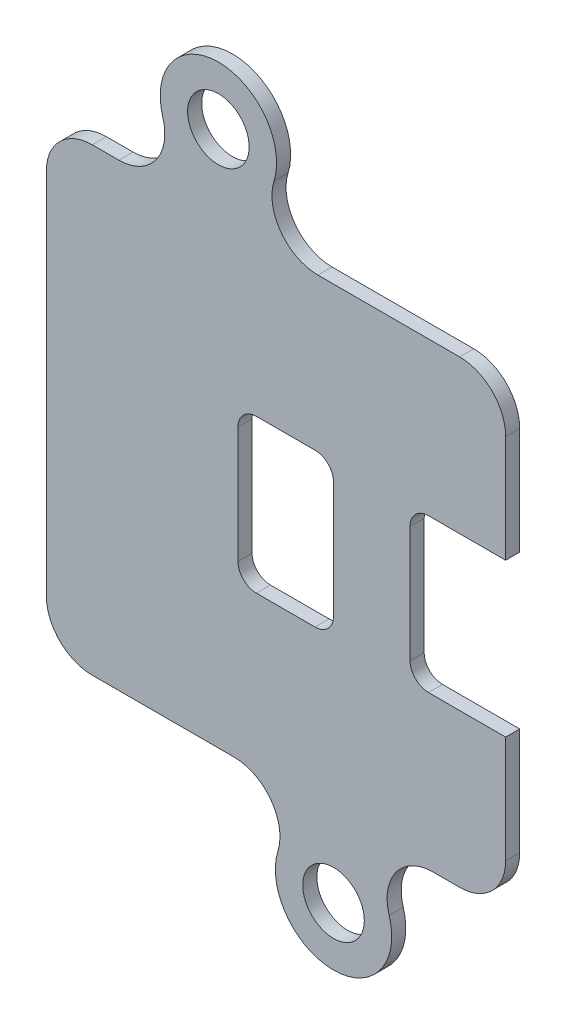
SolidWorks part; units mm, degrees
ref_plane "Front Plane" through (0, 0, 0) normal (0, 0, 1) x (1, 0, 0)
ref_plane "Top Plane" through (0, 0, 0) normal (0, 1, 0) x (1, 0, 0)
ref_plane "Right Plane" through (0, 0, 0) normal (1, 0, 0) x (0, 0, -1)
sketch "Sketch1" plane through (0, 0, 0) normal (0, 0, 1) x (1, 0, 0)
  line L0 (14.2748, 19.05) -> (14.2748, 6.35)
  line L1 (-23.8252, 44.45) -> (-17.8044, 44.45)
  line L2 (-23.8252, 44.45) -> (-23.8252, 6.35)
  line L3 (-23.8252, 6.35) -> (-8.254, 6.35)
  line L4 (14.2748, 44.45) -> (14.2748, 31.75)
  line L5 (14.2748, 31.75) -> (6.35, 31.75)
  line L7 (14.2748, 19.05) -> (6.35, 19.05)
  line L8 (6.35, 31.75) -> (6.35, 19.05)
  line L9 (0, 0) -> (0, 2.5527) construction
  line L10 (0, 0) -> (-50.497, 0) construction
  line L11 (-9.5504, 50.8) -> (-9.5504, 48.2473) construction
  line L12 (0, 31.75) -> (-7.9248, 31.75)
  line L13 (0, 31.75) -> (0, 19.05)
  line L14 (0, 19.05) -> (-7.9248, 19.05)
  line L15 (-7.9248, 31.75) -> (-7.9248, 19.05)
  line L16 (-1.2964, 44.45) -> (14.2748, 44.45)
  line L17 (-9.5504, 44.45) -> (-9.5504, 40.6505) construction
  line L18 (0, 4.826) -> (0, 6.35) construction
  line L19 (8.254, 6.35) -> (14.2748, 6.35)
  line L20 (0, 19.05) -> (0, 44.45) construction
  circle A0 centre (0, 0) radius 2.5527
  circle A1 centre (0, 0) radius 2.5078
  circle A2 centre (-9.5504, 50.8) radius 2.5527
  arc A3 (-4.9379, 49.3806) -> (-14.1629, 49.3806) centre (-9.5504, 50.8) ccw
  arc A4 (-4.6125, 1.4194) -> (4.6125, 1.4194) centre (0, 0) ccw
  arc A5 (-14.1629, 49.3806) -> (-17.8044, 44.45) centre (-17.8044, 48.26) cw
  arc A6 (-4.9379, 49.3806) -> (-1.2964, 44.45) centre (-1.2964, 48.26) ccw
  arc A7 (-4.6125, 1.4194) -> (-8.254, 6.35) centre (-8.254, 2.54) ccw
  arc A8 (4.6125, 1.4194) -> (8.254, 6.35) centre (8.254, 2.54) cw
  dimension "D1" = 5.1054
  dimension "D2" = 9.652
  dimension "D13" = 3.81
  dimension "D14" = 3.81
  dimension "D3" = 9.5504
  dimension "D4" = 50.8
  dimension "D5" = 38.1
  dimension "D6" = 14.2748
  dimension "D7" = 6.35
  dimension "D8" = 6.35
  dimension "D9" = 7.9248
  dimension "D10" = 19.05
  dimension "D11" = 31.75
  dimension "D12" = 7.9248
extrude "Boss-Extrude1" add sketch "Sketch1" along normal mid plane 1.1684 contours A4 A8 L19 L0 L7 L8 L5 L4 L16 A6 A3 A5 L1 L2 L3 A7 L15 L12 L13 L14 A0 A2
fillet "Fillet1" radius 3.81 4 edges at (14.2748, 44.45, 0) (14.2748, 6.35, 0) (-23.8252, 6.35, 0) (-23.8252, 44.45, 0)
fillet "Fillet2" radius 1.524 6 edges at (6.35, 19.05, 0) (6.35, 31.75, 0) (-7.9248, 31.75, 0) (0, 31.75, 0) (0, 19.05, 0) (-7.9248, 19.05, 0)
